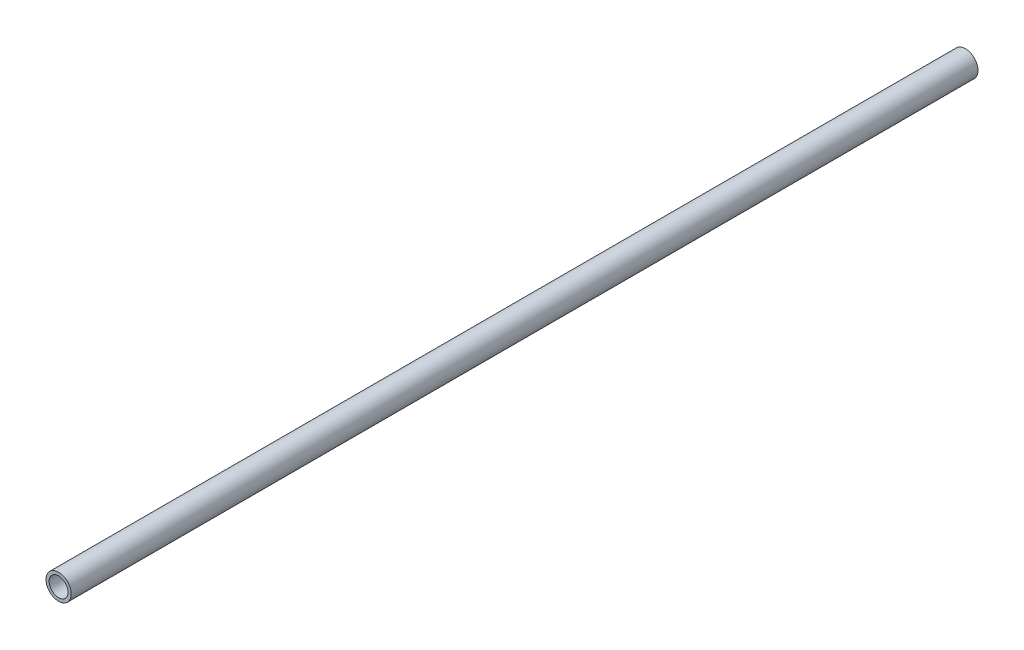
SolidWorks part; units mm, degrees
ref_plane "前视基准面" through (0, 0, 0) normal (0, 0, 1) x (1, 0, 0)
ref_plane "上视基准面" through (0, 0, 0) normal (0, 1, 0) x (1, 0, 0)
ref_plane "右视基准面" through (0, 0, 0) normal (1, 0, 0) x (0, 0, -1)
sketch "草图1" plane through (0, 0, 0) normal (0, 0, 1) x (1, 0, 0)
  circle A0 centre (0, 0) radius 6
  circle A1 centre (0, 0) radius 8
  dimension "D1" = 12
  dimension "D2" = 16
extrude "凸台-拉伸1" add sketch "草图1" along normal blind 575
